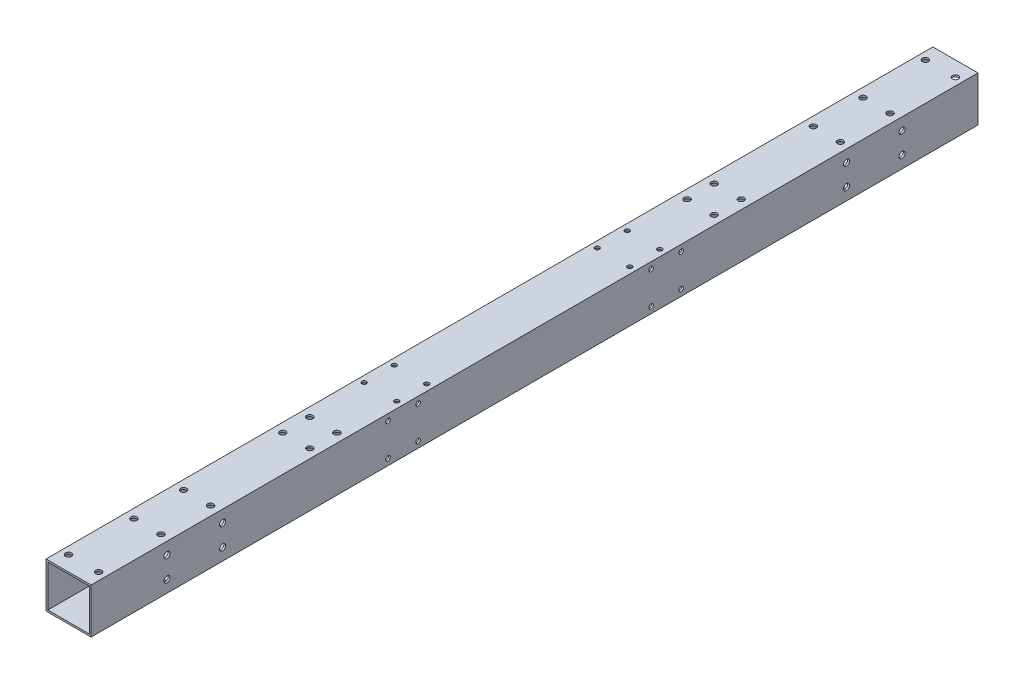
SolidWorks part; units mm, degrees
material "6063-T5"
ref_plane "前视基准面" through (0, 0, 0) normal (0, 0, 1) x (1, 0, 0)
ref_plane "上视基准面" through (0, 0, 0) normal (0, 1, 0) x (1, 0, 0)
ref_plane "右视基准面" through (0, 0, 0) normal (1, 0, 0) x (0, 0, -1)
sketch "草图1" plane through (0, 0, 0) normal (0, 0, 1) x (1, 0, 0)
  line L0 (-13.8, -13.8) -> (-13.8, 13.8)
  line L1 (-15, -15) -> (15, -15)
  line L2 (-15, -15) -> (-15, 15)
  line L3 (-15, 15) -> (15, 15)
  line L4 (15, -15) -> (15, 15)
  line L5 (0, 15) -> (0, -15) construction
  line L6 (-15, 0) -> (15, 0) construction
  line L7 (-13.8, 13.8) -> (13.8, 13.8)
  line L8 (13.8, -13.8) -> (13.8, 13.8)
  line L9 (-13.8, -13.8) -> (13.8, -13.8)
  point P0 (0, 0)
  dimension "D1" = 30
  dimension "D2" = 1.2
extrude "凸台-拉伸1" add sketch "草图1" along normal mid plane 590
sketch "草图2" plane through (0, -15, 0) normal (0, -1, 0) x (1, 0, 0)
  circle A0 centre (-9, 209.5) radius 2.025 construction
  circle A1 centre (9, 209.5) radius 2.025 construction
  circle A2 centre (-9, 242.5) radius 2.025 construction
  circle A3 centre (9, 242.5) radius 2.025 construction
  circle A4 centre (-9, 209.5) radius 2.025
  circle A5 centre (9, 209.5) radius 2.025
  circle A6 centre (-9, 242.5) radius 2.025
  circle A7 centre (9, 242.5) radius 2.025
extrude "切除-拉伸1" cut sketch "草图2" against normal mid plane 70
mirror "镜向1" about plane through (0, 0, 0) normal (0, 0, 1) of "切除-拉伸1"
sketch "草图3" plane through (0, -15, 0) normal (0, -1, 0) x (1, 0, 0)
  circle A0 centre (9, 242.5) radius 3.8
  circle A1 centre (9, 209.5) radius 3.8
  circle A2 centre (-9, 242.5) radius 3.8
  circle A3 centre (-9, 209.5) radius 3.8
  dimension "D1" = 7.6
extrude "切除-拉伸2" cut sketch "草图3" against normal mid plane 10
mirror "镜向2" about plane through (0, 0, 0) normal (0, 0, 1) of "切除-拉伸2"
sketch "草图4" plane through (0, 13.8, 0) normal (0, -1, 0) x (1, 0, 0)
  line L0 (-15, 275) -> (15, 275) construction
  line L1 (-15, 295) -> (-15, -295) construction
  line L2 (15, 295) -> (15, -295) construction
  line L3 (-15, 295) -> (15, 295) construction
  line L4 (15, 295) -> (15, 275) construction
  line L5 (15, 285) -> (-15, 285) construction
  line L6 (0, 285) -> (0, 275) construction
  circle A0 centre (-10, 285) radius 2.025
  circle A1 centre (10, 285) radius 2.025
  dimension "D2" = 4.05
  dimension "D1" = 20
  dimension "D3" = 5
extrude "切除-拉伸3" cut sketch "草图4" against normal mid plane 10
mirror "镜向3" about plane through (0, 0, 0) normal (0, 0, 1) of "切除-拉伸3"
sketch "草图5" plane through (0, -15, 0) normal (0, -1, 0) x (1, 0, 0)
  circle A0 centre (10.8, 67.5) radius 1.525 construction
  circle A1 centre (10.8, 87.5) radius 1.525 construction
  circle A2 centre (10.8, -87.5) radius 1.525 construction
  circle A3 centre (10.8, -67.5) radius 1.525 construction
  circle A4 centre (10.8, 67.5) radius 1.525
  circle A5 centre (10.8, 87.5) radius 1.525
  circle A6 centre (10.8, -87.5) radius 1.525
  circle A7 centre (10.8, -67.5) radius 1.525
extrude "切除-拉伸4" cut sketch "草图5" against normal blind 50
mirror "镜向4" about plane through (0, 0, 0) normal (1, 0, 0) of "切除-拉伸4"
sketch "草图6" plane through (-15, 0, 0) normal (-1, 0, 0) x (0, 0, 1)
  line L0 (0, 0) -> (0, 64.5926) construction
  circle A0 centre (244.5, -7) radius 1.65 construction
  circle A1 centre (244.5, 7) radius 1.65 construction
  circle A2 centre (207.5, -7) radius 1.65 construction
  circle A3 centre (207.5, 7) radius 1.65 construction
  circle A4 centre (244.5, -7) radius 1.65 construction
  circle A5 centre (244.5, 7) radius 1.65 construction
  circle A6 centre (207.5, -7) radius 1.65 construction
  circle A7 centre (207.5, 7) radius 1.65 construction
  circle A8 centre (244.5, 7) radius 2.025
  circle A9 centre (207.5, 7) radius 2.025
  circle A10 centre (207.5, -7) radius 2.025
  circle A11 centre (244.5, -7) radius 2.025
  circle A12 centre (-207.5, 7) radius 1.65 construction
  circle A13 centre (-207.5, -7) radius 1.65 construction
  circle A14 centre (-244.5, 7) radius 1.65 construction
  circle A15 centre (-244.5, -7) radius 1.65 construction
  circle A16 centre (-244.5, -7) radius 2.025
  circle A17 centre (-207.5, -7) radius 2.025
  circle A18 centre (-207.5, 7) radius 2.025
  circle A19 centre (-244.5, 7) radius 2.025
  dimension "D1" = 4.05
extrude "切除-拉伸5" cut sketch "草图6" against normal up to surface (30 mm away) up to face at (15, 0, 0)
sketch "草图7" plane through (0, -15, 0) normal (0, -1, 0) x (1, 0, 0)
  circle A0 centre (-9, 143.5) radius 2.025 construction
  circle A1 centre (-9, 125.5) radius 2.025 construction
  circle A2 centre (9, 125.5) radius 2.025 construction
  circle A3 centre (9, 143.5) radius 2.025 construction
  circle A4 centre (-9, 143.5) radius 2.025
  circle A5 centre (-9, 125.5) radius 2.025
  circle A6 centre (9, 125.5) radius 2.025
  circle A7 centre (9, 143.5) radius 2.025
extrude "切除-拉伸6" cut sketch "草图7" against normal blind 90
mirror "镜向5" about plane through (0, 0, 0) normal (0, 0, 1) of "切除-拉伸6"
sketch "草图8" plane through (0, -15, 0) normal (0, -1, 0) x (1, 0, 0)
  circle A0 centre (-9, -125.5) radius 3.9
  circle A1 centre (-9, -143.5) radius 3.9
  circle A2 centre (9, -143.5) radius 3.9
  circle A3 centre (9, -125.5) radius 3.9
  dimension "D1" = 7.8
extrude "切除-拉伸7" cut sketch "草图8" against normal blind 10
mirror "镜向6" about plane through (0, 0, 0) normal (0, 0, 1) of "切除-拉伸7"
sketch "草图9" plane through (-15, 0, 0) normal (-1, 0, 0) x (0, 0, 1)
  circle A0 centre (97.5, -10.8) radius 1.25 construction
  circle A1 centre (77.5, -10.8) radius 1.25 construction
  circle A2 centre (97.5, -10.8) radius 1.25 construction
  circle A3 centre (77.5, -10.8) radius 1.25 construction
  circle A4 centre (97.5, -10.8) radius 1.525
  circle A5 centre (77.5, -10.8) radius 1.525
  dimension "D1" = 3.05
extrude "切除-拉伸8" cut sketch "草图9" against normal blind 50
mirror "镜向7" about plane through (0, 0, 0) normal (0, 0, 1) of "切除-拉伸8"
mirror "镜向8" about plane through (0, 0, 0) normal (0, 1, 0) of "镜向7", "切除-拉伸8"
